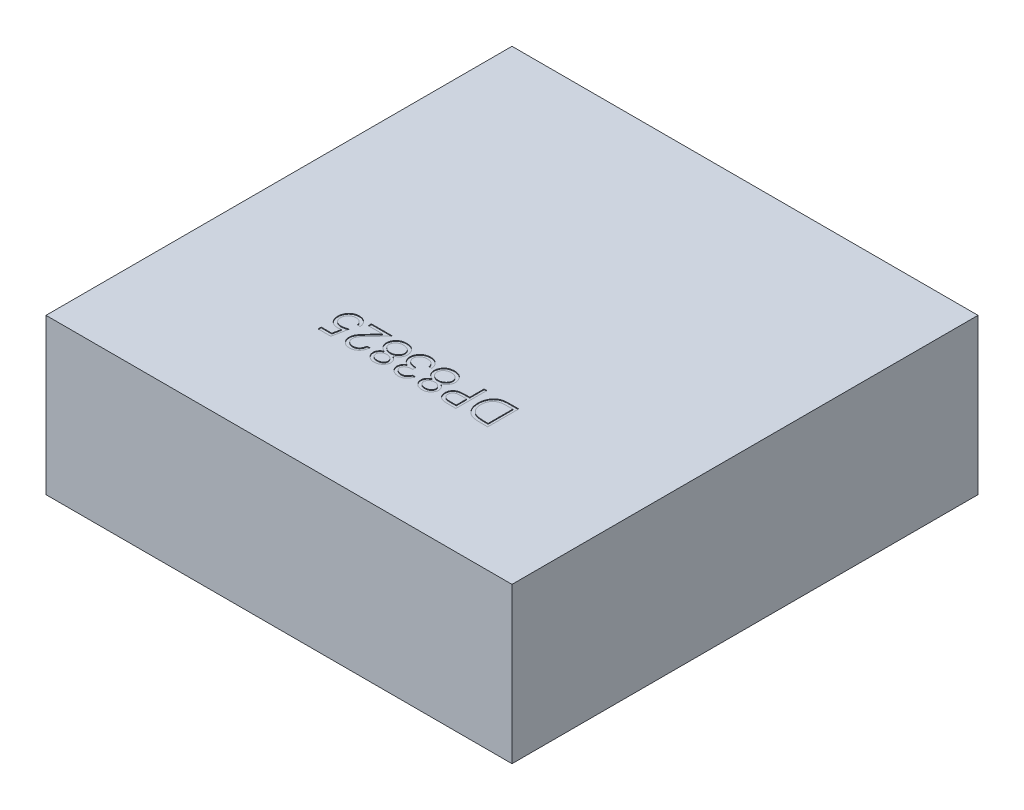
SolidWorks part; units mm, degrees
ref_plane "Front Plane" through (0, 0, 0) normal (0, 0, 1) x (1, 0, 0)
ref_plane "Top Plane" through (0, 0, 0) normal (0, 1, 0) x (1, 0, 0)
ref_plane "Right Plane" through (0, 0, 0) normal (1, 0, 0) x (0, 0, -1)
sketch "BaseS" plane through (0, 0, 0) normal (0, 1, 0) x (1, 0, 0)
  line L1 (-1.5, 1.5) -> (1.5, 1.5)
  line L2 (-1.5, 1.5) -> (-1.5, -1.5)
  line L3 (-1.5, -1.5) -> (1.5, -1.5)
  line L4 (1.5, 1.5) -> (1.5, -1.5)
  line L5 (-1.5, 1.5) -> (1.5, -1.5) construction
  line L6 (-1.5, -1.5) -> (1.5, 1.5) construction
  point P0 (0, 0)
  dimension "Dim" = 3
extrude "Base" add sketch "BaseS" along normal blind 1
sketch "PartNumberS" plane through (0, 1, 0) normal (0, 1, 0) x (1, 0, 0)
  line L0 (1.5, -0.5) -> (-1.5, -0.5) construction
  line L1 (1.5, -1.5) -> (1.5, 1.5) construction
  line L2 (-1.5, 1.5) -> (-1.5, -1.5) construction
  line L3 (-1.5, -1.5) -> (1.5, -1.5) construction
  text T0 "DP83825" font "Century Gothic" height 0.2
  dimension "YDim" = 1
extrude "PartNumber" cut sketch "PartNumberS" against normal blind 0.005
